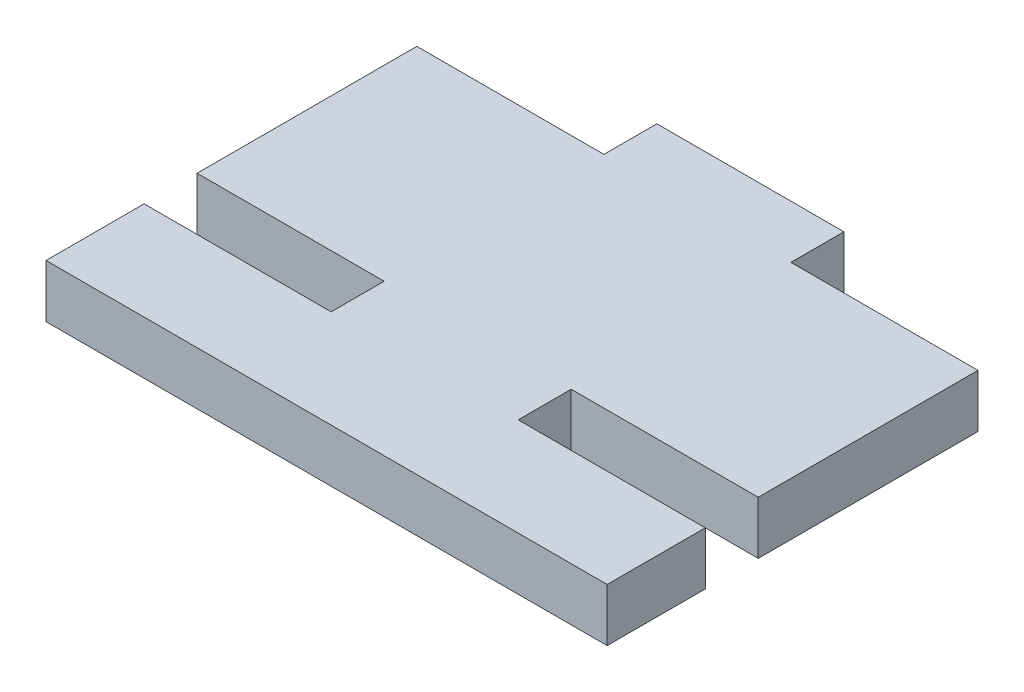
SolidWorks part; units mm, degrees
ref_plane "Front Plane" through (0, 0, 0) normal (0, 0, 1) x (1, 0, 0)
ref_plane "Top Plane" through (0, 0, 0) normal (0, 1, 0) x (1, 0, 0)
ref_plane "Right Plane" through (0, 0, 0) normal (1, 0, 0) x (0, 0, -1)
sketch "Sketch1" plane through (0, 0, 0) normal (0, 1, 0) x (1, 0, 0)
  line L0 (-14.3, -6.95) -> (-4.7667, -6.95)
  line L1 (-4.7667, 9.65) -> (4.7667, 9.65)
  line L2 (-14.3, 6.95) -> (-14.3, -4.25)
  line L3 (-14.3, -11.95) -> (14.3, -11.95)
  line L4 (14.3, 6.95) -> (14.3, -4.25)
  line L5 (-14.3, -4.25) -> (-4.7667, -4.25)
  line L6 (-14.3, 6.95) -> (-4.7667, 6.95)
  line L8 (-14.3, -4.25) -> (14.3, -4.25) construction
  line L9 (4.7667, -4.25) -> (14.3, -4.25)
  line L11 (-14.3, 6.95) -> (14.3, 6.95) construction
  line L12 (4.7667, 6.95) -> (14.3, 6.95)
  line L13 (-4.7667, 6.95) -> (-4.7667, 9.65)
  line L14 (4.7667, 6.95) -> (4.7667, 9.65)
  line L15 (-4.7667, -4.25) -> (-4.7667, -6.95)
  line L16 (4.7667, -4.25) -> (4.7667, -6.95)
  line L17 (-14.3, -6.95) -> (-14.3, -11.95)
  line L18 (14.3, -6.95) -> (14.3, -11.95)
  line L19 (4.7667, -6.95) -> (14.3, -6.95)
  line L20 (-14.3, -6.95) -> (14.3, -6.95) construction
  point P0 (0, 0)
  dimension "D3" = 5
  dimension "D4" = 2.7
  dimension "D5" = 11.2
extrude "Boss-Extrude1" add sketch "Sketch1" along normal blind 2.7
